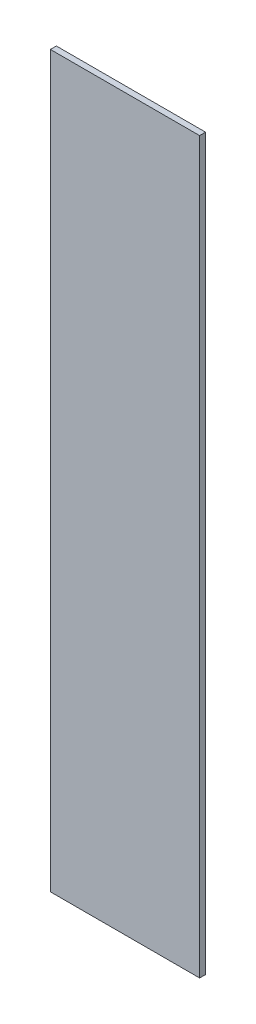
SolidWorks part; units mm, degrees
ref_plane "Front Plane" through (0, 0, 0) normal (0, 0, 1) x (1, 0, 0)
ref_plane "Top Plane" through (0, 0, 0) normal (0, 1, 0) x (1, 0, 0)
ref_plane "Right Plane" through (0, 0, 0) normal (1, 0, 0) x (0, 0, -1)
sketch "Sketch1" plane through (0, 0, 0) normal (0, 0, 1) x (1, 0, 0)
  line L1 (0, 0) -> (450, 0)
  line L2 (0, 0) -> (0, 2200)
  line L3 (0, 2200) -> (450, 2200)
  line L4 (450, 0) -> (450, 2200)
  dimension "D1" = 2200
  dimension "D2" = 450
extrude "Boss-Extrude1" add sketch "Sketch1" along normal blind 18
